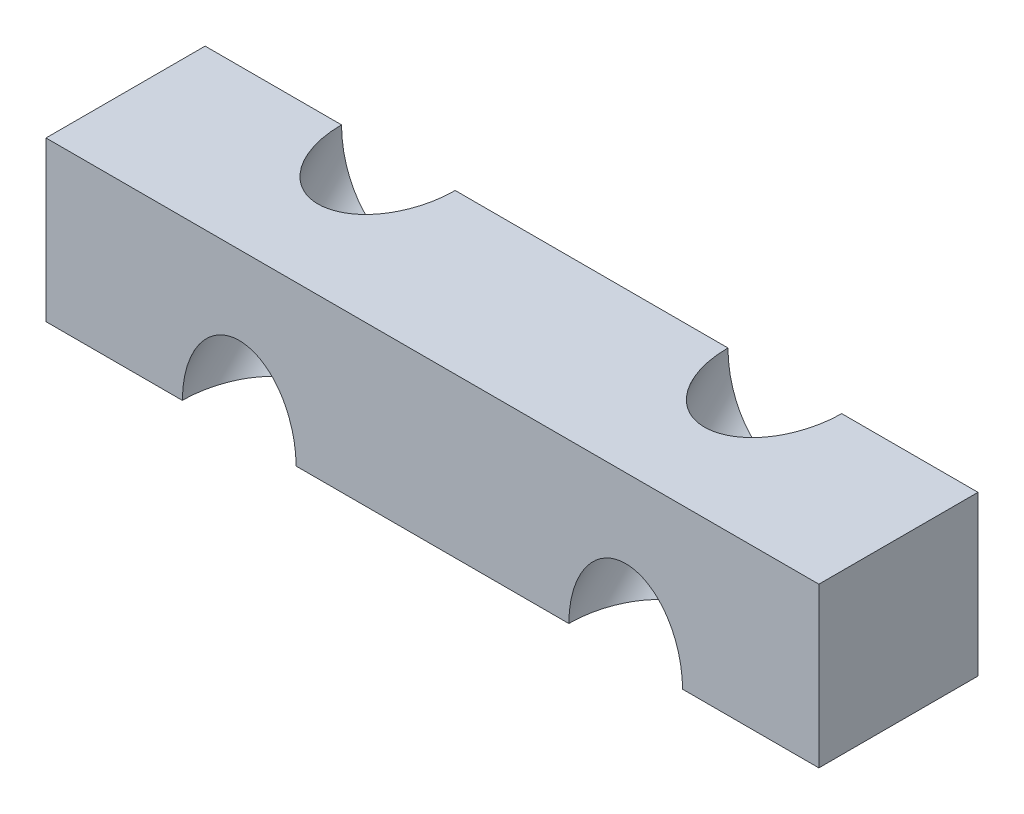
SolidWorks part; units mm, degrees
ref_plane "Front Plane" through (0, 0, 0) normal (0, 0, 1) x (1, 0, 0)
ref_plane "Top Plane" through (0, 0, 0) normal (0, 1, 0) x (1, 0, 0)
ref_plane "Right Plane" through (0, 0, 0) normal (1, 0, 0) x (0, 0, -1)
other "Configuration Table"
sketch "sketch1" plane through (0, 0, 0) normal (0, 1, 0) x (1, 0, 0)
  line L1 (0, 0) -> (34, 0)
  line L2 (0, 0) -> (0, -7)
  line L3 (0, -7) -> (34, -7)
  line L4 (34, 0) -> (34, -7)
  dimension "D1" = 7
  dimension "D2" = 34
extrude "Boss-Extrude1" add sketch "sketch1" along normal blind 7
ref_plane "Plane1" through (0, 0, 0) normal (0, 0.7071, -0.7071) x (-1, 0, 0)
sketch "Sketch6" plane through (0, 0, 0) normal (0, 0.7071, -0.7071) x (-1, 0, 0)
  line L0 (-34, 4.9497) -> (-25.5, 4.9497) construction
  line L1 (0, 0) -> (-34, 0)
  line L2 (0, 0) -> (0, 9.8995)
  line L3 (0, 9.8995) -> (-34, 9.8995)
  line L12 (-34, 0) -> (-34, 9.8995)
  line L13 (-25.5, 4.9497) -> (-8.5, 4.9497) construction
  circle A2 centre (-25.5, 4.9497) radius 2.5
  circle A3 centre (-8.5, 4.9497) radius 2.5
  dimension "D4" = 5
  dimension "D1" = 34
  dimension "D2" = 9.8995
  dimension "D3" = 8.5
  dimension "D6" = 17
  dimension "D5" = 2
extrude "Cut-Extrude2" cut sketch "Sketch6" against normal through all both and the other way through all flip side to cut
equation "\"D2@sketch1\" = \"length\""
equation "\"holes\"= 2"
equation "\"cdist\"= 17mm'centre distance between holes"
equation "\"width\"= 7mm"
equation "\"length\"= \"cdist\" * \"holes\""
equation "\"D1@sketch1\" = \"width\""
equation "\"hdiam\"= 5.00mm'Hole diametre"
equation "\"D4@Sketch6\"=\"hdiam\""
equation "\"D1@Boss-Extrude1\"=\"width\""
equation "\"tolerance\"= 0.04mm"
equation "\"D1@Sketch6\"=\"length\""
equation "\"D2@Sketch6\"=sqr(\"width\"^2 + \"width\"^2)"
equation "\"D3@Sketch6\"=\"cdist\"/2"
equation "\"D5@Sketch6\"=\"holes\""
equation "\"D6@Sketch6\"=\"cdist\""
